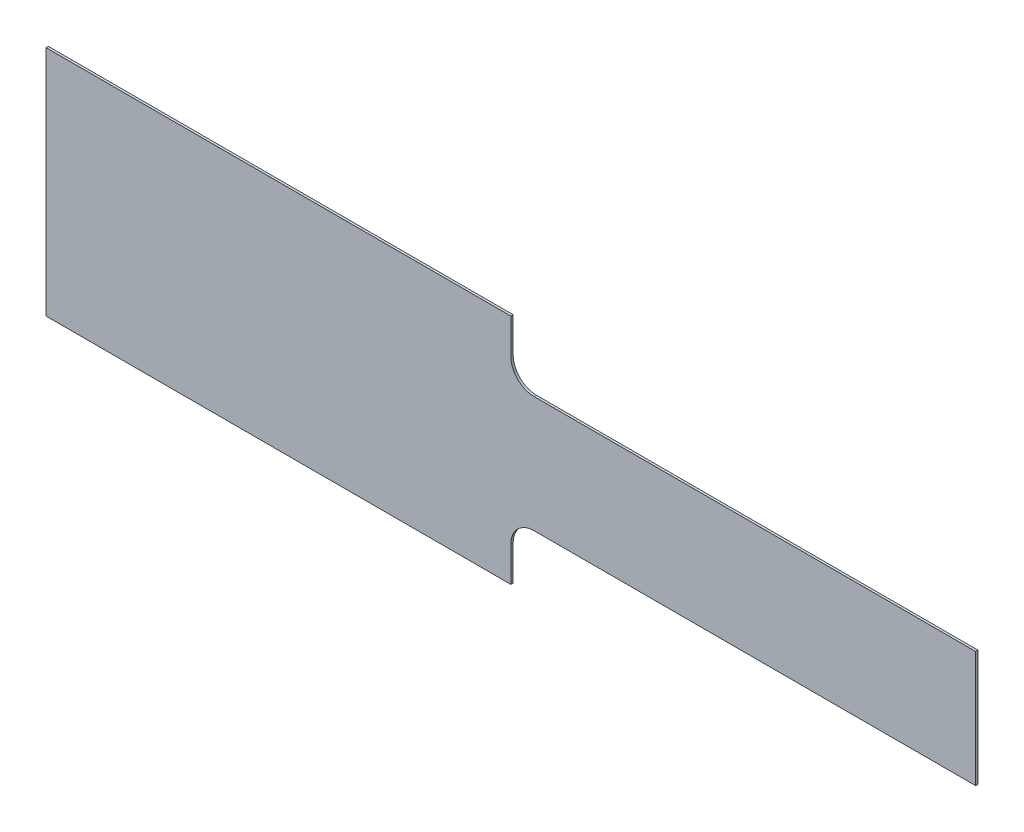
SolidWorks part; units mm, degrees
ref_plane "Ebene vorne" through (0, 0, 0) normal (0, 0, 1) x (1, 0, 0)
ref_plane "Ebene oben" through (0, 0, 0) normal (0, 1, 0) x (1, 0, 0)
ref_plane "Ebene rechts" through (0, 0, 0) normal (1, 0, 0) x (0, 0, -1)
sketch "Skizze1" plane through (0, 0, 0) normal (0, 0, 1) x (1, 0, 0)
  line L1 (0, 50) -> (200, 50)
  line L2 (0, 50) -> (0, -50)
  line L3 (0, -50) -> (200, -50)
  line L4 (200, 50) -> (200, 35)
  line L5 (0, 0) -> (400, 0) construction
  line L6 (210, 25) -> (400, 25)
  line L8 (210, -25) -> (400, -25)
  line L9 (400, 25) -> (400, -25)
  line L10 (200, -35) -> (200, -50)
  arc A0 (210, 25) -> (200, 35) centre (210, 35) cw
  arc A1 (200, -35) -> (210, -25) centre (210, -35) cw
  point P14 (200, 25)
  dimension "D5" = 10
  dimension "D1" = 200
  dimension "D2" = 200
  dimension "D3" = 100
  dimension "D4" = 50
extrude "Linear austragen1" add sketch "Skizze1" along normal blind 1
